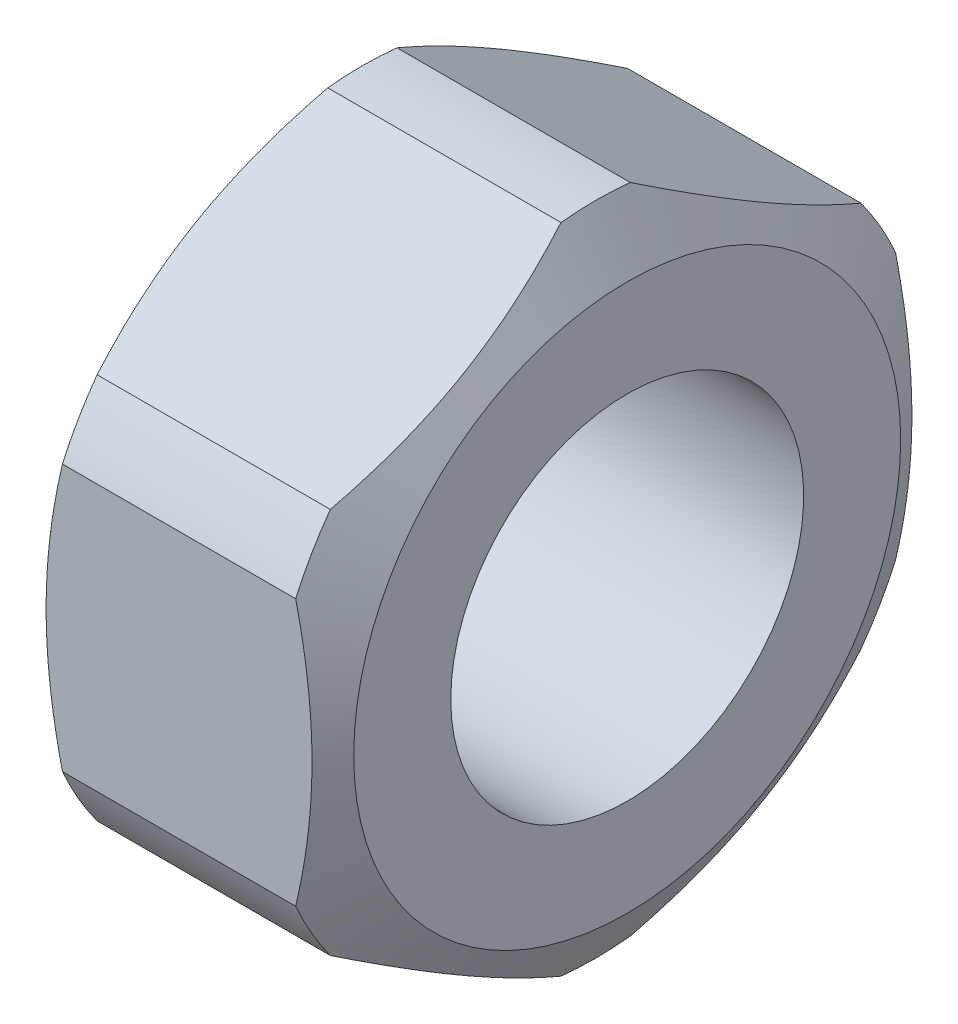
SolidWorks part; units mm, degrees
material "AISI 1020"
ref_plane "Спереди" through (0, 0, 0) normal (0, 0, 1) x (1, 0, 0)
ref_plane "Сверху" through (0, 0, 0) normal (0, 1, 0) x (1, 0, 0)
ref_plane "Справа" through (0, 0, 0) normal (1, 0, 0) x (0, 0, -1)
sketch "Эскиз1" plane through (0, 0, 0) normal (0, 0, 1) x (1, 0, 0)
  line L0 (-345.3781, 0) -> (16923.5283, 0) construction
  line L1 (0, -345.3781) -> (0, 16923.5283) construction
  line L2 (4.2, 5) -> (-4.2, 5)
  line L3 (-4.2, 5) -> (-4.2, 7.75)
  line L4 (-4.2, 7.75) -> (-3.3051, 9.3)
  line L5 (-3.3051, 9.3) -> (3.3051, 9.3)
  line L6 (4.2, 5) -> (4.2, 7.75)
  line L7 (4.2, 7.75) -> (3.3051, 9.3)
  point P11 (0, 5)
  point P13 (0, 9.3)
  dimension "D1" = 30
  dimension "d" = 10
  dimension "m" = 8.4
  dimension "e" = 18.6
  dimension "dw" = 15.5
revolve "Повернуть1" add sketch "Эскиз1" angle 360 about L0
sketch "Эскиз2" plane through (-4.2, 0, 0) normal (-1, 0, 0) x (0, 0, 1)
  line L1 (0, -9.815) -> (8.5, -4.9075)
  line L2 (8.5, -4.9075) -> (8.5, 4.9075)
  line L3 (8.5, 4.9075) -> (0, 9.815)
  line L4 (0, 9.815) -> (-8.5, 4.9075)
  line L5 (-8.5, 4.9075) -> (-8.5, -4.9075)
  line L6 (-8.5, -4.9075) -> (0, -9.815)
  circle A0 centre (0, 0) radius 8.5 construction
  dimension "D1" = 17
extrude "Вырез-Вытянуть1" cut sketch "Эскиз2" against normal through all flip side to cut
